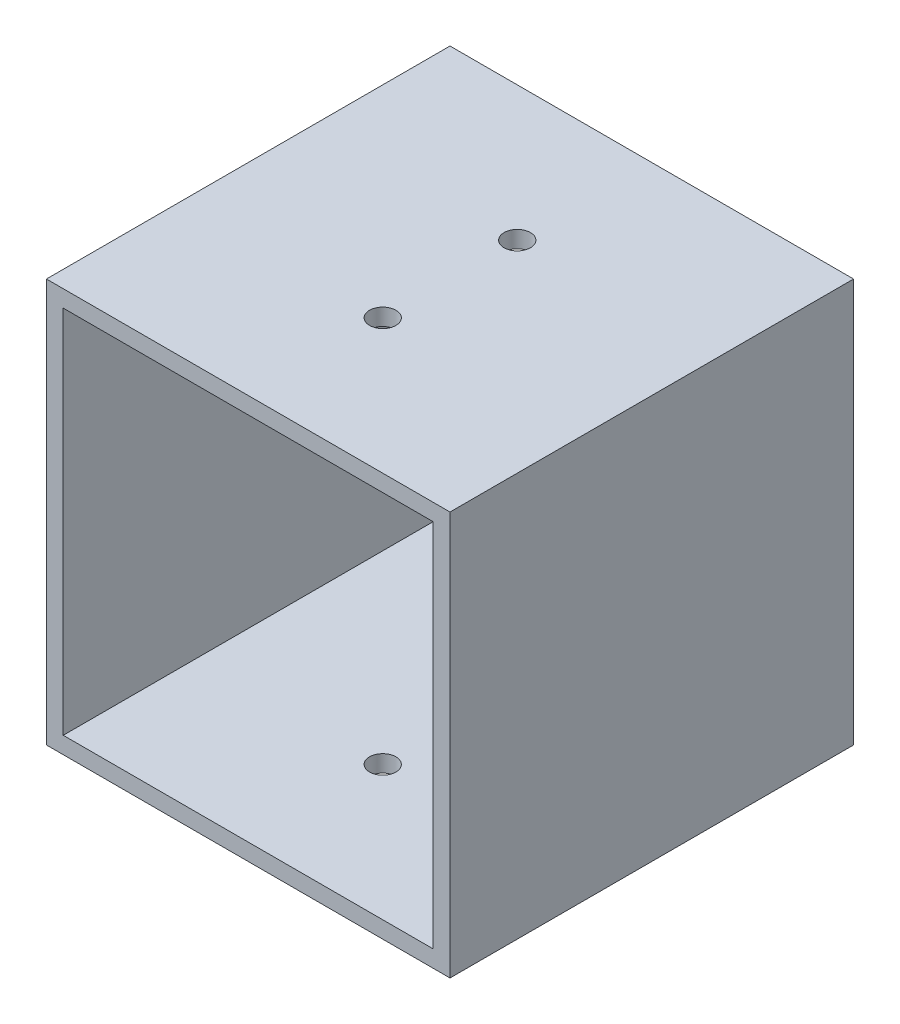
SolidWorks part; units mm, degrees
ref_plane "Front" through (0, 0, 0) normal (0, 0, 1) x (1, 0, 0)
ref_plane "Top" through (0, 0, 0) normal (0, 1, 0) x (1, 0, 0)
ref_plane "Right" through (0, 0, 0) normal (1, 0, 0) x (0, 0, -1)
sketch "Sketch1" plane through (0, 0, 0) normal (0, 0, 1) x (1, 0, 0)
  line L1 (-38.1, -38.1) -> (38.1, -38.1)
  line L2 (-38.1, -38.1) -> (-38.1, 38.1)
  line L3 (-38.1, 38.1) -> (38.1, 38.1)
  line L4 (38.1, -38.1) -> (38.1, 38.1)
  line L5 (-38.1, -38.1) -> (38.1, 38.1) construction
  line L6 (-38.1, 38.1) -> (38.1, -38.1) construction
  point P0 (0, 0)
  dimension "D1" = 76.2
extrude "Extrude-Thin1" add sketch "Sketch1" along normal mid plane 76.2 thin thin type one direction reverse wall 3.175
sketch "Sketch2" plane through (0, -38.1, 0) normal (0, -1, 0) x (1, 0, 0)
  line L0 (0, 38.1) -> (0, -38.1) construction
  line L1 (-38.1, 38.1) -> (38.1, 38.1) construction
  line L2 (-38.1, -38.1) -> (38.1, -38.1) construction
  circle A0 centre (0, 12.7) radius 2.4892
  circle A1 centre (0, -12.7) radius 2.4892
  dimension "D1" = 4.9784
  dimension "D2" = 25.4
  dimension "D3" = 25.4
extrude "Cut-Extrude1" cut sketch "Sketch2" against normal through all
